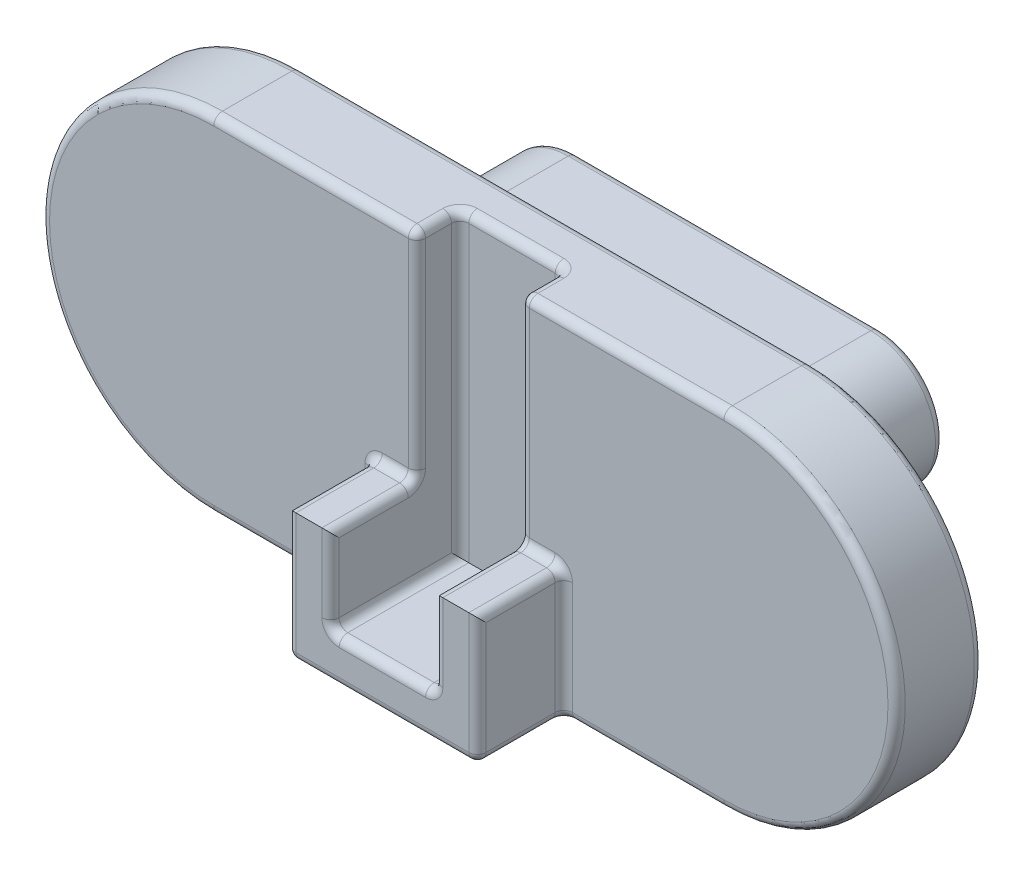
SolidWorks part; units mm, degrees
ref_plane "Płaszczyzna przednia" through (0, 0, 0) normal (0, 0, 1) x (1, 0, 0)
ref_plane "Płaszczyzna górna" through (0, 0, 0) normal (0, 1, 0) x (1, 0, 0)
ref_plane "Płaszczyzna prawa" through (0, 0, 0) normal (1, 0, 0) x (0, 0, -1)
sketch "Szkic1" plane through (0, 0, 0) normal (0, 0, 1) x (1, 0, 0)
  line L0 (0, 0) -> (5.9, 0) construction
  line L1 (0, 2) -> (5.9, 2)
  line L2 (0, -2) -> (5.9, -2)
  arc A0 (0, 2) -> (0, -2) centre (0, 0) ccw
  arc A1 (5.9, -2) -> (5.9, 2) centre (5.9, 0) ccw
  point P3 (2.95, 0)
  point P8 (7.9, 0)
  point P9 (-2, 0)
  dimension "D1" = 4
  dimension "D2" = 9.9
extrude "Dodanie-wyciągnięcie1" add sketch "Szkic1" along normal blind 1
sketch "Szkic2" plane through (0, 0, 0) normal (0, 0, -1) x (-1, 0, 0)
  line L0 (-1.2, 0) -> (-4.7, 0) construction
  line L1 (-1.2, -0.75) -> (-4.7, -0.75)
  line L2 (-1.2, 0.75) -> (-4.7, 0.75)
  line L3 (-5.9, 2) -> (0, 2) construction
  line L4 (0, 0) -> (-5.9, 0) construction
  arc A0 (-1.2, -0.75) -> (-1.2, 0.75) centre (-1.2, 0) ccw
  arc A1 (-4.7, 0.75) -> (-4.7, -0.75) centre (-4.7, 0) ccw
  point P3 (-2.95, 0)
  point P8 (0, 0)
  point P11 (-2.95, 2)
  point P12 (0, 0)
  point P13 (0, 0)
  point P14 (0, 0)
  point P15 (0, 0)
  point P16 (0, 0)
  point P17 (-5.45, 0)
  point P18 (-0.45, 0)
  dimension "D1" = 1.5
  dimension "D2" = 5
extrude "Dodanie-wyciągnięcie2" add sketch "Szkic2" along normal blind 2
sketch "Szkic3" plane through (0, 0, 1) normal (0, 0, 1) x (1, 0, 0)
  line L0 (2.95, 2) -> (2.95, -2) construction
  line L1 (5.9, 2) -> (0, 2) construction
  line L2 (0, -2) -> (5.9, -2) construction
  line L3 (2.35, -1.5) -> (3.55, -1.5)
  line L4 (2.35, -1.5) -> (2.35, -0.5)
  line L5 (3.55, -1.5) -> (3.55, -0.5)
  line L6 (4.05, -2) -> (4.05, -0.5)
  line L7 (1.85, -2) -> (4.05, -2)
  line L8 (1.85, -2) -> (1.85, -0.5)
  line L9 (2.35, -0.5) -> (1.85, -0.5)
  line L10 (3.55, -0.5) -> (4.05, -0.5)
  point P9 (2.95, -1.5)
  dimension "D1" = 1.2
  dimension "D2" = 0.5
  dimension "D3" = 1
  dimension "D4" = 0.5
extrude "Dodanie-wyciągnięcie3" add sketch "Szkic3" along normal blind 1
sketch "Szkic4" plane through (0, 2, 0) normal (0, 1, 0) x (1, 0, 0)
  line L0 (2.35, 0) -> (2.35, -1.4014) construction
  line L1 (5.9, 0) -> (0, 0) construction
  line L2 (2.35, -2) -> (2.35, -1) construction
  line L3 (3.55, -1.2144) -> (3.55, 0) construction
  line L4 (3.55, -2) -> (3.55, -1) construction
  line L5 (5.9, -1) -> (0, -1) construction
  line L6 (3.55, -0.5) -> (2.35, -0.5)
  line L7 (3.55, -0.5) -> (3.55, -1)
  line L8 (3.55, -1) -> (2.35, -1)
  line L9 (2.35, -0.5) -> (2.35, -1)
  dimension "D1" = 0.5
extrude "Wytnij-wyciągnięcie1" cut sketch "Szkic4" against normal up to surface (3.5 mm away) up to face at (2.95, -1.5, 1.5)
fillet "Zaokrąglenie1" radius 0.1 43 edges at (4.05, -1.25, 1) (1.85, -1.25, 1) (3.55, -1, 2) (2.35, -1, 2) (0.45, 0, -2) (2.95, -0.75, -2) (5.45, 0, -2) (4.975, -2, 1) (7.9, 0, 1) (0.925, -2, 1) (-2, 0, 1) (2.95, -2, 0) (7.9, 0, 0) (2.95, 2, 0) (-2, 0, 0) (3.8, -0.5, 1) (2.1, -0.5, 1) (1.85, -1.25, 2) (1.85, -0.5, 1.5) (4.05, -0.5, 1.5) (4.05, -1.25, 2) (4.05, -2, 1.5) (1.85, -2, 1.5) (2.95, -2, 2) (3.55, -0.5, 1.5) (2.35, -0.5, 1.5) (3.55, -1.5, 1.25) (2.95, -1.5, 2) (2.35, -1.5, 1.25) (3.55, 0.75, 1) (3.55, 0.25, 0.5) (2.35, 0.75, 1) (2.35, 0.25, 0.5) (2.95, 0.75, -2) (3.55, 2, 0.75) (2.35, 2, 0.75) (2.95, 2, 0.5) (4.725, 2, 1) (1.175, 2, 1) (0.45, 0, 0) (2.95, -0.75, 0) (5.45, 0, 0) (2.95, 0.75, 0)
